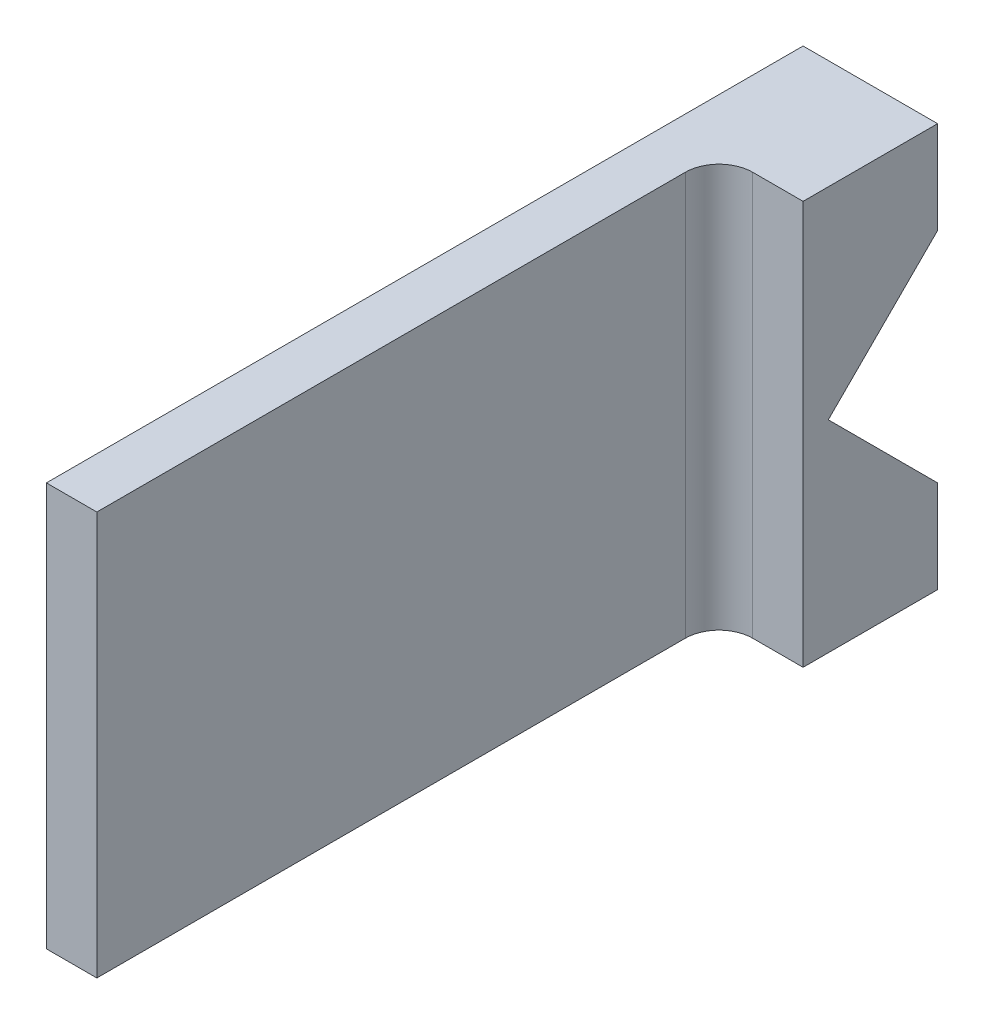
SolidWorks part; units mm, degrees
ref_plane "Front Plane" through (0, 0, 0) normal (0, 0, 1) x (1, 0, 0)
ref_plane "Top Plane" through (0, 0, 0) normal (0, 1, 0) x (1, 0, 0)
ref_plane "Right Plane" through (0, 0, 0) normal (1, 0, 0) x (0, 0, -1)
sketch "Sketch1" plane through (0, 0, 0) normal (1, 0, 0) x (0, 0, -1)
  line L0 (0, -10.3187) -> (0, -19.05)
  line L1 (0, -19.05) -> (-71.4375, -19.05)
  line L2 (-71.4375, -19.05) -> (-71.4375, 19.05)
  line L3 (-71.4375, 19.05) -> (0, 19.05)
  line L4 (0, 19.05) -> (0, 10.3187)
  line L5 (0, 0) -> (-71.4375, 0) construction
  line L6 (0, -10.3187) -> (-10.3187, 0)
  line L7 (-10.3187, 0) -> (0, 10.3187)
  dimension "D2" = 20.6375
  dimension "D1" = 38.1
  dimension "D3" = 71.4375
  dimension "D4" = 10.3187
extrude "Boss-Extrude1" add sketch "Sketch1" along normal blind 12.7
sketch "Sketch2" plane through (0, 19.05, 0) normal (0, 1, 0) x (1, 0, 0)
  line L0 (12.7, -12.7) -> (4.7625, -12.7)
  line L1 (12.7, 0) -> (12.7, -71.4375) construction
  line L2 (4.7625, -12.7) -> (4.7625, -71.4375)
  line L3 (12.7, -71.4375) -> (0, -71.4375) construction
  line L4 (4.7625, -71.4375) -> (12.7, -71.4375)
  line L5 (12.7, -71.4375) -> (12.7, -12.7)
  line L6 (0, 0) -> (0, -71.4375) construction
  line L7 (12.7, 0) -> (0, 0) construction
  dimension "D1" = 4.7625
  dimension "D2" = 12.7
extrude "Cut-Extrude1" cut sketch "Sketch2" against normal through all
fillet "Fillet1" radius 3.175 1 edges at (4.7625, 0, 12.7)
